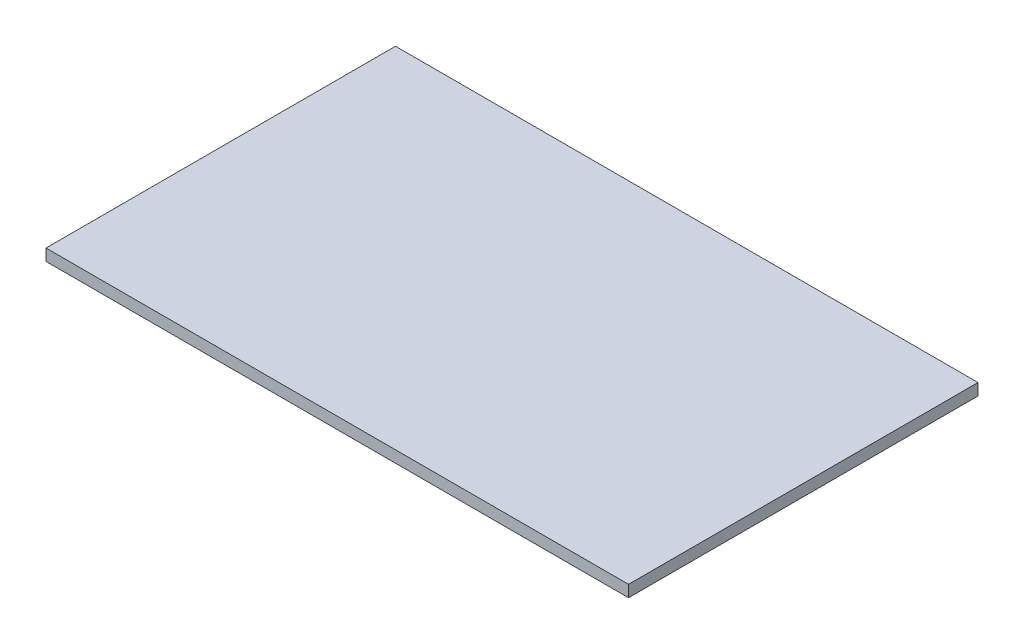
SolidWorks part; units mm, degrees
ref_plane "Plan de face" through (0, 0, 0) normal (0, 0, 1) x (1, 0, 0)
ref_plane "Plan de dessus" through (0, 0, 0) normal (0, 1, 0) x (1, 0, 0)
ref_plane "Plan de droite" through (0, 0, 0) normal (1, 0, 0) x (0, 0, -1)
sketch "Esquisse1" plane through (0, 0, 0) normal (0, 1, 0) x (1, 0, 0)
  line L1 (0, 0) -> (500, 0)
  line L2 (0, 0) -> (0, 300)
  line L3 (0, 300) -> (500, 300)
  line L4 (500, 0) -> (500, 300)
  dimension "D1" = 300
  dimension "D2" = 500
extrude "Boss.-Extru.1" add sketch "Esquisse1" along normal blind 10
